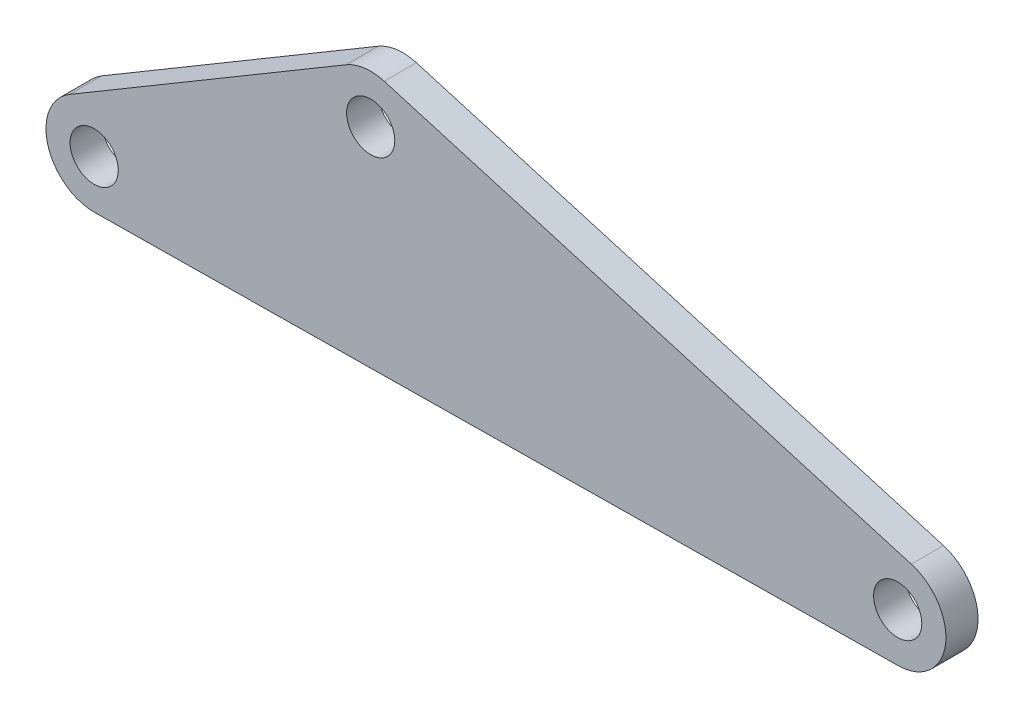
SolidWorks part; units mm, degrees
ref_plane "Front Plane" through (0, 0, 0) normal (0, 0, 1) x (1, 0, 0)
ref_plane "Top Plane" through (0, 0, 0) normal (0, 1, 0) x (1, 0, 0)
ref_plane "Right Plane" through (0, 0, 0) normal (1, 0, 0) x (0, 0, -1)
sketch "Sketch2" plane through (0, 0, 0) normal (0, 0, 1) x (1, 0, 0)
  line L3 (-188.968, -4.5878) -> (-49.181, 78.2827)
  line L4 (-49.181, 78.2827) -> (217.2679, 0.0983)
  line L5 (217.2679, 0.0983) -> (-188.968, -4.5878)
  line L6 (-133.164, 11.0569) -> (-47.1439, 62.0525) construction
  line L7 (-47.1439, 62.0525) -> (116.8194, 13.9406) construction
  line L8 (116.8194, 13.9406) -> (-133.164, 11.0569) construction
  circle A0 centre (-133.164, 11.0569) radius 7.5
  circle A1 centre (-47.1439, 62.0525) radius 7.5
  circle A2 centre (116.8194, 13.9406) radius 7.5
  dimension "D5" = 15
  dimension "D6" = 15
  dimension "D7" = 15
  dimension "D1" = 250
  dimension "D2" = 100
  dimension "D3" = 30
extrude "Boss-Extrude1" add sketch "Sketch2" along normal blind 10
fillet "Fillet1" radius 15 1 edges at (217.2679, 0.0983, 5)
fillet "Fillet2" radius 15 1 edges at (-49.181, 78.2827, 5)
fillet "Fillet3" radius 15 1 edges at (-188.968, -4.5878, 5)
